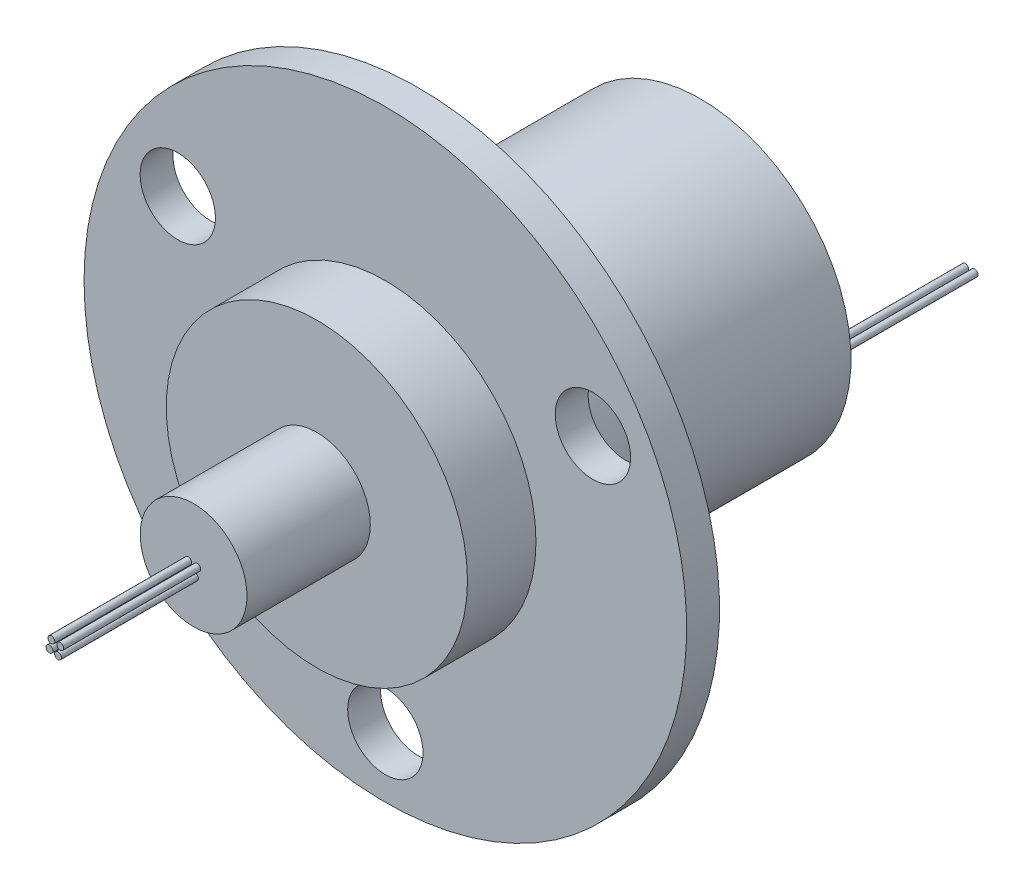
SolidWorks part; units mm, degrees
ref_plane "Front Plane" through (0, 0, 0) normal (0, 0, 1) x (1, 0, 0)
ref_plane "Top Plane" through (0, 0, 0) normal (0, 1, 0) x (1, 0, 0)
ref_plane "Right Plane" through (0, 0, 0) normal (1, 0, 0) x (0, 0, -1)
ref_plane "Plane1" through (0, 0, 0) normal (0, -1, 0) x (1, 0, 0)
sketch "Sketch1" plane through (0, 0, 0) normal (0, -1, 0) x (1, 0, 0)
  line L0 (22, 2.4) -> (0, 2.4)
  line L1 (0, 2.4) -> (0, 0)
  line L2 (0, 0) -> (22, 0)
  line L3 (22, 0) -> (22, 2.4)
  line L4 (0, 2.4) -> (0, 0) construction
revolve "Revolve1" add sketch "Sketch1" angle 360 about L4
sketch "Sketch2" plane through (0, 0, 2.4) normal (0, 0, 1) x (1, 0, 0)
  circle A0 centre (0, 0) radius 11
extrude "Boss-Extrude1" add sketch "Sketch2" along normal blind 5
sketch "Sketch3" plane through (0, 0, 7.4) normal (0, 0, 1) x (1, 0, 0)
  circle A0 centre (0, 0) radius 3.9
extrude "Boss-Extrude2" add sketch "Sketch3" along normal blind 9
sketch "Sketch4" plane through (0, 0, 0) normal (0, 0, -1) x (-1, 0, 0)
  circle A0 centre (0, 0) radius 11
extrude "Boss-Extrude3" add sketch "Sketch4" along normal blind 20.6
ref_plane "Plane2" through (0, -0.6758, 0) normal (0, -1, 0) x (1, 0, 0)
sketch "Sketch5" plane through (0, -0.6758, 0) normal (0, -1, 0) x (1, 0, 0)
  line L0 (0.3481, 26.4) -> (0.0981, 26.4)
  line L1 (0.0981, 26.4) -> (0.0981, 16.4)
  line L2 (0.0981, 16.4) -> (0.3481, 16.4)
  line L3 (0.3481, 16.4) -> (0.3481, 26.4)
  line L4 (0.0981, 26.4) -> (0.0981, 16.4) construction
revolve "Revolve2" add sketch "Sketch5" angle 360 about L4
ref_plane "Plane3" through (0, 0.0912, 0) normal (0, -1, 0) x (1, 0, 0)
sketch "Sketch6" plane through (0, 0.0912, 0) normal (0, -1, 0) x (1, 0, 0)
  line L0 (-0.1352, 26.4) -> (-0.3852, 26.4)
  line L1 (-0.3852, 26.4) -> (-0.3852, 16.4)
  line L2 (-0.3852, 16.4) -> (-0.1352, 16.4)
  line L3 (-0.1352, 16.4) -> (-0.1352, 26.4)
  line L4 (-0.3852, 26.4) -> (-0.3852, 16.4) construction
revolve "Revolve3" add sketch "Sketch6" angle 360 about L4
ref_plane "Plane4" through (0, -0.5625, 0) normal (0, -1, 0) x (1, 0, 0)
sketch "Sketch7" plane through (0, -0.5625, 0) normal (0, -1, 0) x (1, 0, 0)
  line L0 (-0.2774, 26.4) -> (-0.5274, 26.4)
  line L1 (-0.5274, 26.4) -> (-0.5274, 16.4)
  line L2 (-0.5274, 16.4) -> (-0.2774, 16.4)
  line L3 (-0.2774, 16.4) -> (-0.2774, 26.4)
  line L4 (-0.5274, 26.4) -> (-0.5274, 16.4) construction
revolve "Revolve4" add sketch "Sketch7" angle 360 about L4
sketch "Sketch8" plane through (0, 0, 0) normal (0, 1, 0) x (1, 0, 0)
  line L0 (-9.0139, 30.6) -> (-9.2639, 30.6)
  line L1 (-9.2639, 30.6) -> (-9.2639, 20.6)
  line L2 (-9.2639, 20.6) -> (-9.0139, 20.6)
  line L3 (-9.0139, 20.6) -> (-9.0139, 30.6)
  line L4 (-9.2639, 30.6) -> (-9.2639, 20.6) construction
revolve "Revolve5" add sketch "Sketch8" angle 360 about L4
sketch "Sketch9" plane through (0, 0, 0) normal (0, 1, 0) x (1, 0, 0)
  line L0 (10.2742, 30.6) -> (10.0242, 30.6)
  line L1 (10.0242, 30.6) -> (10.0242, 20.6)
  line L2 (10.0242, 20.6) -> (10.2742, 20.6)
  line L3 (10.2742, 20.6) -> (10.2742, 30.6)
  line L4 (10.0242, 30.6) -> (10.0242, 20.6) construction
revolve "Revolve6" add sketch "Sketch9" angle 360 about L4
sketch "Sketch10" plane through (0, 0, 0) normal (0, 1, 0) x (1, 0, 0)
  line L0 (9.5943, 30.6) -> (9.3443, 30.6)
  line L1 (9.3443, 30.6) -> (9.3443, 20.6)
  line L2 (9.3443, 20.6) -> (9.5943, 20.6)
  line L3 (9.5943, 20.6) -> (9.5943, 30.6)
  line L4 (9.3443, 30.6) -> (9.3443, 20.6) construction
revolve "Revolve7" add sketch "Sketch10" angle 360 about L4
sketch "Sketch11" plane through (0, 0, 0) normal (0, 1, 0) x (1, 0, 0)
  line L0 (-9.8523, 30.6) -> (-10.1023, 30.6)
  line L1 (-10.1023, 30.6) -> (-10.1023, 20.6)
  line L2 (-10.1023, 20.6) -> (-9.8523, 20.6)
  line L3 (-9.8523, 20.6) -> (-9.8523, 30.6)
  line L4 (-10.1023, 30.6) -> (-10.1023, 20.6) construction
revolve "Revolve8" add sketch "Sketch11" angle 360 about L4
sketch "Sketch12" plane through (0, 0, 0) normal (0, -1, 0) x (1, 0, 0)
  line L0 (0.5138, 26.4) -> (0.2638, 26.4)
  line L1 (0.2638, 26.4) -> (0.2638, 16.4)
  line L2 (0.2638, 16.4) -> (0.5138, 16.4)
  line L3 (0.5138, 16.4) -> (0.5138, 26.4)
  line L4 (0.2638, 26.4) -> (0.2638, 16.4) construction
revolve "Revolve9" add sketch "Sketch12" angle 360 about L4
hole_wizard "Ø5.5 (5.5) Diameter Hole1" positions "Sketch14" profile "Sketch13" hole size "Ø5.5" standard "ANSI Metric"
sketch "Sketch14" plane through (0, 0, 0) normal (0, 0, -1) x (-1, 0, 0)
  point P0 (-15.1554, 8.75)
  point P1 (15.1554, 8.75)
  point P2 (0, -17.5)
sketch "Sketch13" plane through (15.1554, 8.75, 0) normal (1, 0, 0) x (0, 1, 0)
  line L0 (0, 0) -> (0, 26.4)
  line L1 (0, 26.4) -> (2.75, 26.4)
  line L2 (2.75, 26.4) -> (2.75, 0)
  line L5 (2.75, 0) -> (0, 0)
  line L11 (0, -6.35) -> (0, 107.95) construction
  dimension "Thru Hole Dia." = 5.5
  dimension "Thru Hole Depth" = 26.4
